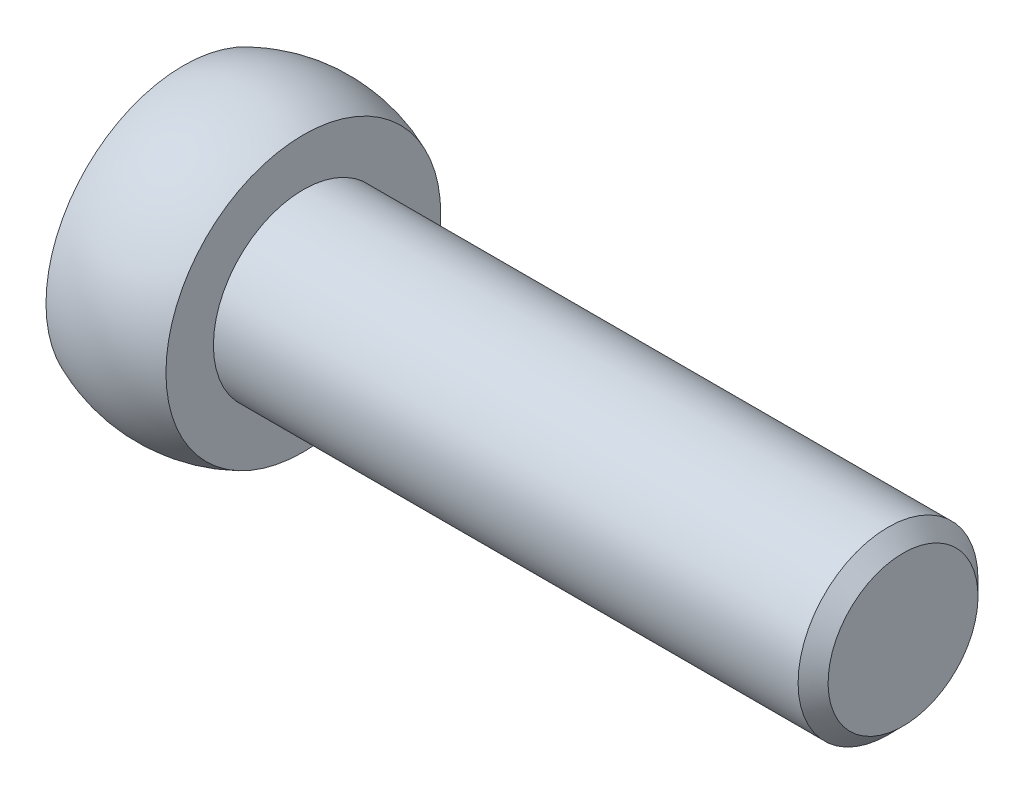
SolidWorks part; units mm, degrees
ref_plane "Спереди" through (0, 0, 0) normal (0, 0, 1) x (1, 0, 0)
ref_plane "Сверху" through (0, 0, 0) normal (0, 1, 0) x (1, 0, 0)
ref_plane "Справа" through (0, 0, 0) normal (1, 0, 0) x (0, 0, -1)
sketch "Эскиз1" plane through (0, 0, 0) normal (0, 0, 1) x (1, 0, 0)
  line L0 (0, 0) -> (0, 4.5826)
  line L1 (0, 0) -> (-1.604, 0) construction
  line L2 (4, 4.5826) -> (4, 3)
  line L3 (4, 3) -> (23.5, 3)
  line L4 (24, 2.5) -> (24, 0)
  line L5 (24, 0) -> (0, 0)
  line L6 (3, 5) -> (0, 5) construction
  line L7 (23.5, 3) -> (24, 2.5)
  arc A0 (0, 4.5826) -> (4, 4.5826) centre (2, 0) cw
  point P6 (24, 3)
  dimension "D5" = 5
  dimension "D6" = 2
  dimension "D1" = 24
  dimension "D2" = 6
  dimension "D3" = 4
  dimension "D4" = 5
  dimension "D7" = 0.5
  dimension "D8" = 45
revolve "Повернуть1" add sketch "Эскиз1" angle 360 about L1
